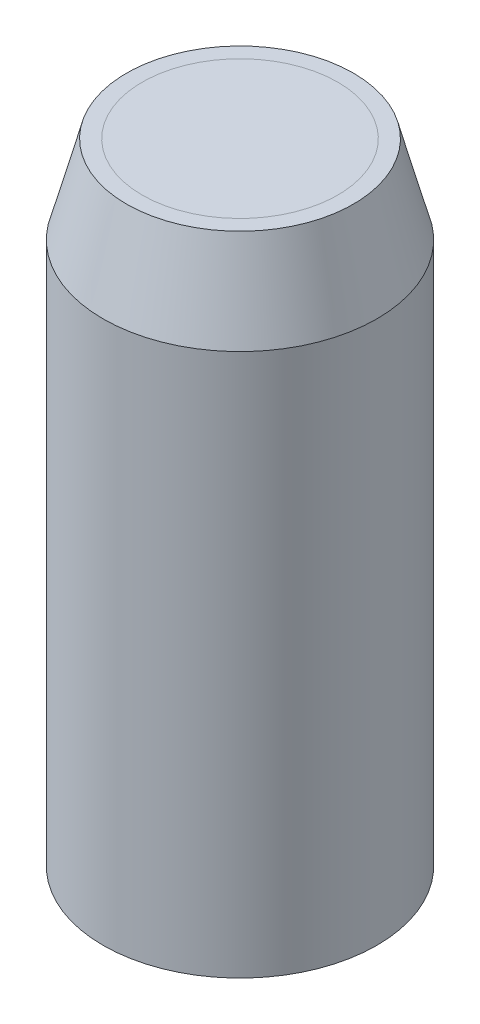
SolidWorks part; units mm, degrees
material "PLA"
ref_plane "Front Plane" through (0, 0, 0) normal (0, 0, 1) x (1, 0, 0)
ref_plane "Top Plane" through (0, 0, 0) normal (0, 1, 0) x (1, 0, 0)
ref_plane "Right Plane" through (0, 0, 0) normal (1, 0, 0) x (0, 0, -1)
sketch "Sketch1" plane through (0, 0, 0) normal (0, 1, 0) x (1, 0, 0)
  circle A0 centre (0, 0) radius 5
  dimension "D1" = 10
extrude "Boss-Extrude1" add sketch "Sketch1" along normal blind 29.8117
sketch "Sketch2" plane through (0, 0, 0) normal (0, 0, 1) x (1, 0, 0)
  line L0 (0, 0) -> (-5, 0)
  line L1 (-5, 0) -> (5, 0) construction
  line L2 (-5, 0) -> (-5, 29.8117)
  line L3 (-5, 29.8117) -> (-5.8, 29.8117)
  line L4 (-5.8, 29.8117) -> (-7, 25.3333)
  line L5 (-7, 25.3333) -> (-7, -2.4)
  line L6 (-7, -2.4) -> (0, -2.4)
  line L7 (0, -2.4) -> (0, 0)
  line L8 (-5, 29.8117) -> (-5, 0) construction
  line L9 (5, 29.8117) -> (-5, 29.8117) construction
  line L10 (0, 0) -> (0, 29.8117) construction
  dimension "D1" = 2
  dimension "D2" = 2.4
  dimension "D3" = 15
  dimension "D4" = 0.8
revolve "Revolve1" add sketch "Sketch2" angle 360 about L10
equation "\"Charge mass\"= 1.5'Mass in grams"
equation "\"Charge volume\"= \"Charge mass\" / 0.000640642'Volume in mm^3"
equation "\"Charge height\"= \"Charge volume\" / ( pi * ( 5 ) ^ 2 )"
equation "\"D1@Boss-Extrude1\"= \"Charge height\""
